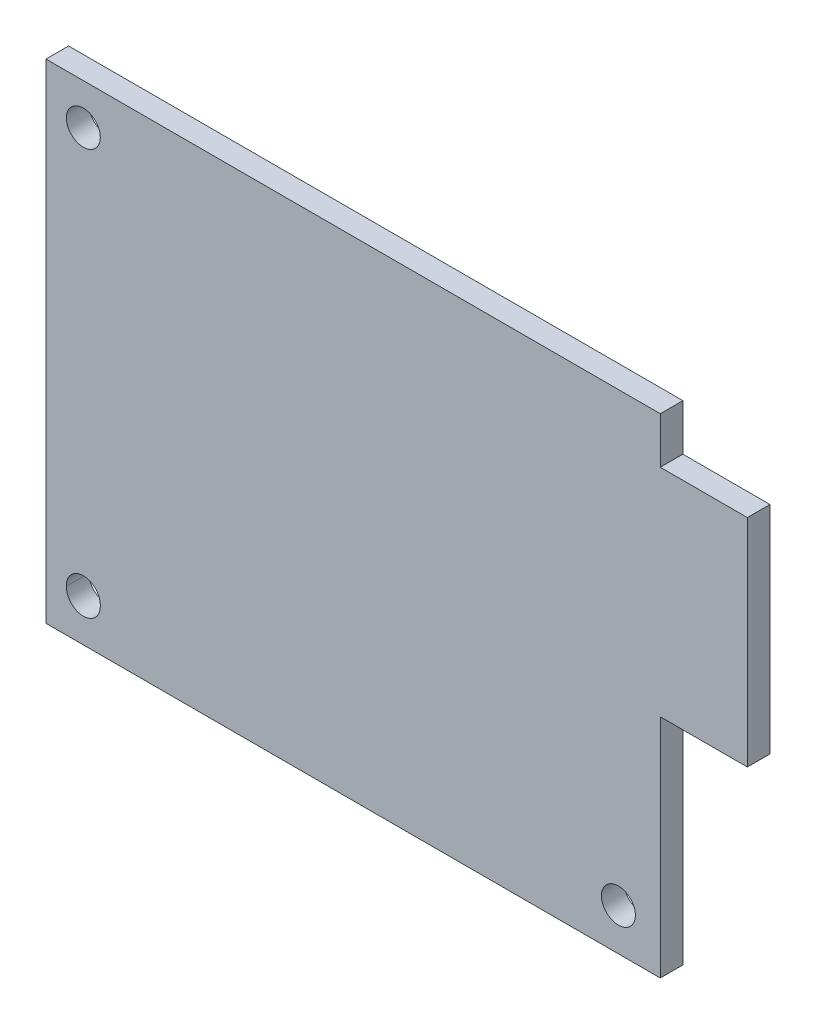
SolidWorks part; units mm, degrees
ref_plane "Plan de face" through (0, 0, 0) normal (0, 0, 1) x (1, 0, 0)
ref_plane "Plan de dessus" through (0, 0, 0) normal (0, 1, 0) x (1, 0, 0)
ref_plane "Plan de droite" through (0, 0, 0) normal (1, 0, 0) x (0, 0, -1)
sketch "Esquisse1" plane through (0, 0, 0) normal (0, 0, 1) x (1, 0, 0)
  line L0 (27.15, 17.5) -> (34.85, 17.5)
  line L1 (-27.15, 21.6) -> (27.15, 21.6)
  line L2 (-27.15, 21.6) -> (-27.15, -21.6)
  line L3 (-27.15, -21.6) -> (27.15, -21.6)
  line L4 (27.15, 21.6) -> (27.15, 17.5)
  line L5 (-27.15, 21.6) -> (27.15, -21.6) construction
  line L6 (-27.15, -21.6) -> (27.15, 21.6) construction
  line L7 (34.85, 17.5) -> (34.85, -1.6)
  line L8 (34.85, -1.6) -> (27.15, -1.6)
  line L9 (27.15, -1.6) -> (27.15, -21.6)
  point P0 (0, 0)
  dimension "D1" = 54.3
  dimension "D2" = 43.2
  dimension "D3" = 19.1
  dimension "D4" = 4.1
  dimension "D5" = 62
extrude "Boss.-Extru.1" add sketch "Esquisse1" along normal blind 2
hole_wizard "Dégagement M3.51" positions "Esquisse2" profile "Esquisse3" hole size "M3.5" standard "Ansi Metric" end condition up to next
sketch "Esquisse2" plane through (0, 0, 2) normal (0, 0, 1) x (1, 0, 0)
  line L0 (27.15, -21.6) -> (27.15, -1.6) construction
  line L1 (-27.15, -21.6) -> (27.15, -21.6) construction
  point P0 (-23.85, 18)
  point P2 (-23.85, -17.9)
  point P4 (-23.85, -17.8)
  point P7 (23.45, -17.9)
  dimension "D1" = 47.3
  dimension "D2" = 35.9
  dimension "D3" = 3.7
  dimension "D4" = 3.7
sketch "Esquisse3" plane through (-23.85, 18, 2) normal (1, 0, 0) x (0, -1, 0)
  line L0 (0, 0) -> (0, 2)
  line L1 (0, 2) -> (1.5, 2)
  line L2 (1.5, 2) -> (1.5, 0)
  line L5 (1.5, 0) -> (0, 0)
  line L11 (0, -6.35) -> (0, 107.95) construction
  dimension "Diamètre du perçage jusqu'au prochain" = 3
  dimension "Profondeur du perçage jusqu'au prochain" = 2
